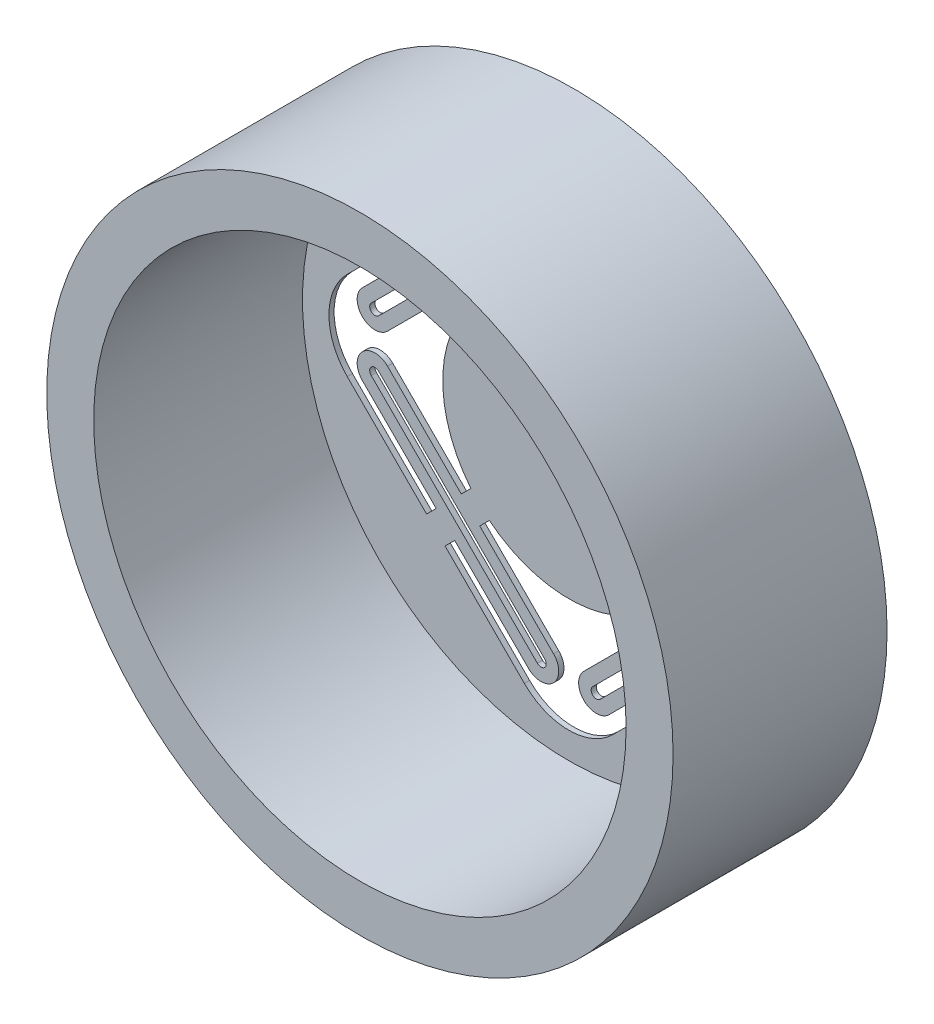
SolidWorks part; units mm, degrees
ref_plane "Front Plane" through (0, 0, 0) normal (0, 0, 1) x (1, 0, 0)
ref_plane "Top Plane" through (0, 0, 0) normal (0, 1, 0) x (1, 0, 0)
ref_plane "Right Plane" through (0, 0, 0) normal (1, 0, 0) x (0, 0, -1)
sketch "Sketch1" plane through (0, 0, 0) normal (0, 0, 1) x (1, 0, 0)
  circle A0 centre (0, 0) radius 15
  circle A1 centre (0, 0) radius 12.75
extrude "Boss-Extrude1" add sketch "Sketch1" along normal blind 10
sketch "Sketch2" plane through (0, 0, 0) normal (0, 0, 1) x (1, 0, 0)
  line L0 (-12.7279, 0) -> (0, -12.7279) construction
  line L1 (-12.7279, 0) -> (0, 12.7279) construction
  line L2 (0, -12.7279) -> (12.7279, 0) construction
  line L3 (0, 12.7279) -> (12.7279, 0) construction
  line L4 (-6.364, 6.364) -> (6.364, -6.364) construction
  line L5 (5.2923, 5.3143) -> (9.0999, 1.5067) construction
  line L6 (6.364, 6.364) -> (-6.364, -6.364) construction
  line L7 (5.922, 5.0381) -> (5.0381, 5.922)
  line L8 (5.922, 5.0381) -> (9.4576, 1.5026)
  line L9 (6.3463, 5.4624) -> (9.8818, 1.9268)
  line L10 (6.3463, 5.4624) -> (6.8059, 5.922)
  line L11 (5.0381, 5.922) -> (1.5026, 9.4576)
  line L12 (5.4624, 6.3463) -> (1.9268, 9.8818)
  line L13 (5.4624, 6.3463) -> (5.922, 6.8059)
  line L14 (5.5685, 4.6846) -> (4.6846, 5.5685)
  line L15 (5.5685, 4.6846) -> (9.104, 1.149)
  line L16 (5.1442, 4.2603) -> (8.6798, 0.7248)
  line L17 (5.1442, 4.2603) -> (4.6846, 3.8007)
  line L18 (4.2603, 5.1442) -> (3.8007, 4.6846)
  line L19 (4.2603, 5.1442) -> (0.7248, 8.6798)
  line L20 (4.6846, 5.5685) -> (1.149, 9.104)
  line L21 (-12.7279, 0) -> (12.7279, 0) construction
  line L22 (0, -12.7279) -> (0, 12.7279) construction
  line L23 (-5.4624, 6.3463) -> (-5.922, 6.8059)
  line L24 (-5.4624, 6.3463) -> (-1.9268, 9.8818)
  line L25 (-5.5685, 4.6846) -> (-9.104, 1.149)
  line L26 (-5.922, 5.0381) -> (-9.4576, 1.5026)
  line L27 (-5.922, 5.0381) -> (-5.0381, 5.922)
  line L28 (-5.0381, 5.922) -> (-1.5026, 9.4576)
  line L29 (-4.6846, 5.5685) -> (-1.149, 9.104)
  line L30 (-5.5685, 4.6846) -> (-4.6846, 5.5685)
  line L31 (-4.2603, 5.1442) -> (-0.7248, 8.6798)
  line L32 (-4.2603, 5.1442) -> (-3.8007, 4.6846)
  line L33 (-6.3463, 5.4624) -> (-6.8059, 5.922)
  line L34 (-6.3463, 5.4624) -> (-9.8818, 1.9268)
  line L35 (-5.2923, 5.3143) -> (-9.0999, 1.5067) construction
  line L36 (-5.1442, 4.2603) -> (-8.6798, 0.7248)
  line L37 (-5.1442, 4.2603) -> (-4.6846, 3.8007)
  line L38 (6.3463, -5.4624) -> (9.8818, -1.9268)
  line L39 (5.4624, -6.3463) -> (5.922, -6.8059)
  line L40 (6.3463, -5.4624) -> (6.8059, -5.922)
  line L41 (5.1442, -4.2603) -> (8.6798, -0.7248)
  line L42 (5.1442, -4.2603) -> (4.6846, -3.8007)
  line L43 (4.2603, -5.1442) -> (3.8007, -4.6846)
  line L44 (5.4624, -6.3463) -> (1.9268, -9.8818)
  line L45 (4.2603, -5.1442) -> (0.7248, -8.6798)
  line L46 (5.2923, -5.3143) -> (9.0999, -1.5067) construction
  line L47 (5.5685, -4.6846) -> (9.104, -1.149)
  line L48 (5.922, -5.0381) -> (9.4576, -1.5026)
  line L49 (5.922, -5.0381) -> (5.0381, -5.922)
  line L50 (5.0381, -5.922) -> (1.5026, -9.4576)
  line L51 (4.6846, -5.5685) -> (1.149, -9.104)
  line L52 (5.5685, -4.6846) -> (4.6846, -5.5685)
  line L53 (-5.4624, -6.3463) -> (-1.9268, -9.8818)
  line L54 (-5.4624, -6.3463) -> (-5.922, -6.8059)
  line L55 (-4.2603, -5.1442) -> (-0.7248, -8.6798)
  line L56 (-4.2603, -5.1442) -> (-3.8007, -4.6846)
  line L57 (-5.1442, -4.2603) -> (-8.6798, -0.7248)
  line L58 (-5.1442, -4.2603) -> (-4.6846, -3.8007)
  line L59 (-6.3463, -5.4624) -> (-6.8059, -5.922)
  line L60 (-6.3463, -5.4624) -> (-9.8818, -1.9268)
  line L61 (-5.2923, -5.3143) -> (-9.0999, -1.5067) construction
  line L62 (-5.5685, -4.6846) -> (-4.6846, -5.5685)
  line L63 (-4.6846, -5.5685) -> (-1.149, -9.104)
  line L64 (-5.0381, -5.922) -> (-1.5026, -9.4576)
  line L65 (-5.922, -5.0381) -> (-5.0381, -5.922)
  line L66 (-5.922, -5.0381) -> (-9.4576, -1.5026)
  line L67 (-5.5685, -4.6846) -> (-9.104, -1.149)
  line L68 (-6.8059, 5.922) -> (-12.7279, 0)
  line L69 (-12.7279, 0) -> (-6.8059, -5.922)
  line L70 (-5.922, -6.8059) -> (0, -12.7279)
  line L71 (0, -12.7279) -> (5.922, -6.8059)
  line L72 (6.8059, -5.922) -> (12.7279, 0)
  line L73 (12.7279, 0) -> (6.8059, 5.922)
  line L74 (5.922, 6.8059) -> (0, 12.7279)
  line L75 (0, 12.7279) -> (-5.922, 6.8059)
  circle A0 centre (0, 0) radius 15
  circle A1 centre (0, 0) radius 12.7279 construction
  arc A2 (9.4576, 1.5026) -> (9.104, 1.149) centre (9.2808, 1.3258) cw
  arc A3 (9.8818, 1.9268) -> (8.6798, 0.7248) centre (9.2808, 1.3258) cw
  arc A4 (1.5026, 9.4576) -> (1.149, 9.104) centre (1.3258, 9.2808) ccw
  arc A5 (1.9268, 9.8818) -> (0.7248, 8.6798) centre (1.3258, 9.2808) ccw
  arc A6 (-1.9268, 9.8818) -> (-0.7248, 8.6798) centre (-1.3258, 9.2808) cw
  arc A7 (-9.4576, 1.5026) -> (-9.104, 1.149) centre (-9.2808, 1.3258) ccw
  arc A8 (-1.5026, 9.4576) -> (-1.149, 9.104) centre (-1.3258, 9.2808) cw
  arc A9 (-9.8818, 1.9268) -> (-8.6798, 0.7248) centre (-9.2808, 1.3258) ccw
  arc A10 (9.8818, -1.9268) -> (8.6798, -0.7248) centre (9.2808, -1.3258) ccw
  arc A11 (9.4576, -1.5026) -> (9.104, -1.149) centre (9.2808, -1.3258) ccw
  arc A12 (1.5026, -9.4576) -> (1.149, -9.104) centre (1.3258, -9.2808) cw
  arc A13 (1.9268, -9.8818) -> (0.7248, -8.6798) centre (1.3258, -9.2808) cw
  arc A14 (-1.9268, -9.8818) -> (-0.7248, -8.6798) centre (-1.3258, -9.2808) ccw
  arc A15 (-9.8818, -1.9268) -> (-8.6798, -0.7248) centre (-9.2808, -1.3258) cw
  arc A16 (-1.5026, -9.4576) -> (-1.149, -9.104) centre (-1.3258, -9.2808) ccw
  arc A17 (-9.4576, -1.5026) -> (-9.104, -1.149) centre (-9.2808, -1.3258) cw
  arc A18 (-3.8007, 4.6846) -> (3.8007, 4.6846) centre (0, 0) cw
  arc A19 (-4.6846, 3.8007) -> (-4.6846, -3.8007) centre (0, 0) ccw
  arc A20 (-3.8007, -4.6846) -> (3.8007, -4.6846) centre (0, 0) ccw
  arc A21 (4.6846, 3.8007) -> (4.6846, -3.8007) centre (0, 0) cw
  point P25 (5.4801, 5.4801)
  dimension "D1" = 18
  dimension "D2" = 1.5
  dimension "D3" = 0.25
  dimension "D4" = 5
  dimension "D5" = 0.6
  dimension "D6" = 18
extrude "Boss-Extrude2" add sketch "Sketch2" against normal blind 0.25 contours A0 A21 L17 L16 A3 L9 L10 L73 L72 L40 L38 A10 L41 L42 A18 L32 L31 A6 L24 L23 L75 L74 L13 L12 A5 L19 L18 A4 L11 L7 L8 A2 L15 L14 L20 L28 A8 L29 L30 L25 A7 L26 L27 L50 A12 L51
fillet "Fillet1" radius 3 4 edges at (0, 12.7279, -0.125) (-12.7279, 0, -0.125) (0, -12.7279, -0.125) (12.7279, 0, -0.125)
